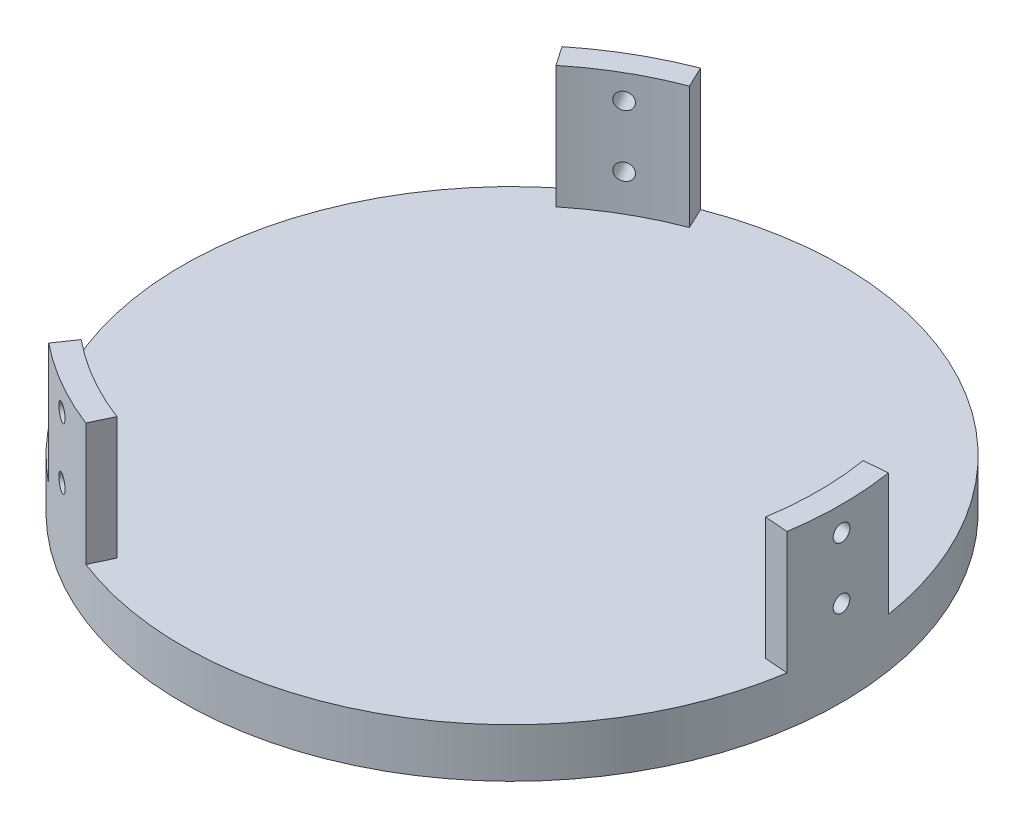
SolidWorks part; units mm, degrees
material "6061-T6 (SS)"
ref_plane "Front" through (0, 0, 0) normal (0, 0, 1) x (1, 0, 0)
ref_plane "Top" through (0, 0, 0) normal (0, 1, 0) x (1, 0, 0)
ref_plane "Right" through (0, 0, 0) normal (1, 0, 0) x (0, 0, -1)
sketch "Sketch1" plane through (0, 0, 0) normal (0, 1, 0) x (1, 0, 0)
  line L1 (0, 0) -> (127.635, 0)
  line L2 (0, 0) -> (0, 127.635)
  line L3 (0, 127.635) -> (127.635, 127.635)
  line L4 (127.635, 0) -> (127.635, 127.635)
  dimension "D1" = 127.635
  dimension "D2" = 127.635
extrude "Main Plate" add sketch "Sketch1" along normal blind 12.7
sketch "Sketch9" plane through (0, 12.7, 0) normal (0, 1, 0) x (1, 0, 0)
  circle A0 centre (63.8175, 63.8175) radius 85.725
  dimension "D1" = 171.45
extrude "Boss-Extrude1" add sketch "Sketch9" against normal up to surface (12.7 mm away) contours A0 up to face at (63.8175, 0, -63.8175)
sketch "Sketch10" plane through (0, 12.7, 0) normal (0, 1, 0) x (1, 0, 0)
  circle A0 centre (63.8175, 63.8175) radius 95.25
  circle A1 centre (63.8175, 63.8175) radius 85.4075
  dimension "D1" = 170.815
  dimension "D2" = 190.5
extrude "Cut-Extrude1" cut sketch "Sketch10" against normal blind 167.64 contours A0 | A1
sketch "Sketch14" plane through (0, 12.7, 0) normal (0, 1, 0) x (1, 0, 0)
  line L0 (201.1692, 63.8175) -> (-73.4523, 63.8175) construction
ref_plane "Plane1" through (0, 0, -63.8175) normal (0, 0, -1) x (-1, 0, 0)
ref_plane "Plane3" through (0, 6.35, 0) normal (0, 1, 0) x (1, 0, 0)
ref_plane "Plane2" through (-21.59, 0, 0) normal (-1, 0, 0) x (0, 0, 1)
sketch "Sketch18" plane through (0, 6.35, 0) normal (0, 1, 0) x (1, 0, 0)
  circle A0 centre (63.8175, 63.8175) radius 85.4075
  circle A1 centre (63.8175, 63.8175) radius 79.375
  circle A4 centre (63.8175, 63.8175) radius 85.4075 construction
  dimension "D1" = 158.75
extrude "Boss-Extrude2" add sketch "Sketch18" along normal blind 38.1
sketch "Sketch20" plane through (0, 12.7, 0) normal (0, 1, 0) x (1, 0, 0)
  line L0 (63.8175, 143.1925) -> (63.8175, -15.5575) construction
  line L1 (-15.5575, 63.8175) -> (143.1925, 63.8175) construction
  line L2 (63.8175, 63.8175) -> (-15.5575, -73.664) construction
  circle A0 centre (63.8175, 63.8175) radius 79.375 construction
  dimension "D1" = 30
ref_plane "Plane5" through (-15.5575, 12.7, 73.664) normal (-0.5, 0, 0.866) x (0.866, 0, 0.5)
sketch "Sketch15" plane through (166.2216, 0, 178.6143) normal (0.5, 0, -0.866) x (-0.866, 0, -0.5)
  line L3 (289.2754, 44.45) -> (130.5254, 44.45) construction
  circle A0 centre (209.9004, 22.225) radius 2.159
  circle A1 centre (209.9004, 38.1) radius 2.159
  dimension "D1" = 4.318
  dimension "D2" = 15.875
  dimension "D3" = 4.318
  dimension "D6" = 6.35
extrude "Cut-Extrude3" cut sketch "Sketch15" along normal blind 88.9
pattern_circular "CirPattern1" count 3 over 360 about axis through (63.8175, -154.94, -63.8175) along (0, 1, 0) of "Cut-Extrude3"
ref_plane "Plane4" through (63.8175, 0, 0) normal (-1, 0, 0) x (0, 0, 1)
sketch "Sketch23" plane through (0, 12.7, 0) normal (0, 1, 0) x (1, 0, 0)
  line L0 (13.6787, 125.352) -> (7.5523, 134.2379)
  line L1 (15.1867, 11.8815) -> (13.6787, 2.283) construction
  line L3 (-15.5575, 63.8175) -> (143.1925, 63.8175) construction
  line L4 (63.8175, 143.1925) -> (63.8175, -15.5575) construction
  line L5 (-15.5575, 63.8175) -> (143.1925, 63.8175)
  line L6 (63.8175, 143.1925) -> (63.8175, -15.5575)
  line L7 (13.6787, 2.283) -> (6.9592, -7.4631)
  line L8 (-19.2671, 125.3206) -> (-48.797, 60.3978)
  line L9 (-48.797, 60.3978) -> (-9.8843, 7.0525)
  line L10 (-9.8843, 7.0525) -> (6.9592, -7.4631)
  line L11 (24.1345, -4.9259) -> (13.6787, 2.283) construction
  line L14 (7.5523, 134.2379) -> (-19.2671, 125.3206)
  line L15 (24.1345, 132.5609) -> (13.6787, 125.352) construction
  line L28 (63.8175, 63.8175) -> (24.1345, -4.9259) construction
  line L29 (63.8175, 63.8175) -> (24.1345, 132.5609) construction
  line L30 (142.1773, 76.4717) -> (152.9359, 77.3344)
  line L31 (152.9359, 77.3344) -> (158.6231, 105.0193)
  line L32 (158.6231, 105.0193) -> (117.1632, 163.0543)
  line L33 (117.1632, 163.0543) -> (51.5085, 156.0277)
  line L34 (51.5085, 156.0277) -> (30.5159, 148.6985)
  line L35 (35.5964, 138.0062) -> (30.5159, 148.6985)
  line L36 (35.5964, -10.3712) -> (30.9643, -20.1198)
  line L37 (30.9643, -20.1198) -> (52.0965, -38.8874)
  line L38 (52.0965, -38.8874) -> (123.0863, -31.9996)
  line L39 (123.0863, -31.9996) -> (149.8284, 28.3723)
  line L40 (149.8284, 28.3723) -> (153.9775, 50.217)
  line L41 (142.1773, 51.1633) -> (153.9775, 50.217)
  circle A0 centre (63.8175, 63.8175) radius 79.375 construction
  arc A1 (13.6787, 2.283) -> (13.6787, 125.352) centre (63.8175, 63.8175) cw
  circle A3 centre (63.8175, 63.8175) radius 79.375
  arc A6 (35.5964, 138.0062) -> (142.1773, 76.4717) centre (63.8175, 63.8175) cw
  arc A7 (142.1773, 51.1633) -> (35.5964, -10.3712) centre (63.8175, 63.8175) cw
  circle A9 centre (63.8175, 63.8175) radius 79.375
  dimension "D1" = 79.375
  dimension "D2" = 0
  dimension "D3" = 12.7
  dimension "D4" = 90
  dimension "D5" = 12.7
  dimension "D6" = 90
  dimension "D8" = 60.004
  dimension "D9" = 60.004
  dimension "D7" = 3
extrude "Cut-Extrude6" cut sketch "Sketch23" along normal blind 111.6
